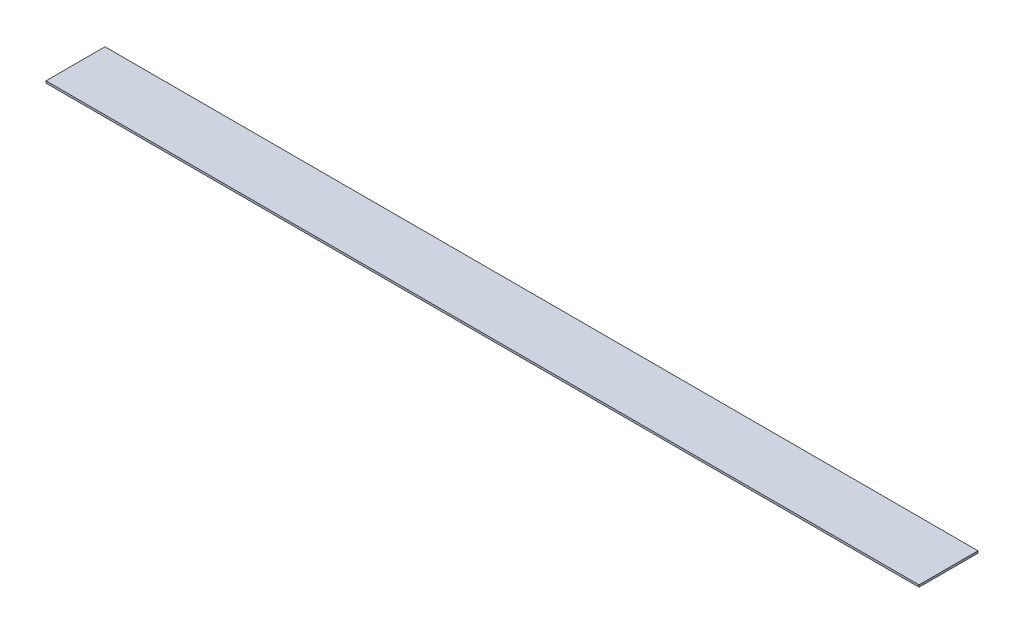
SolidWorks part; units mm, degrees
material "201 Annealed Stainless Steel (SS)"
ref_plane "Front Plane" through (0, 0, 0) normal (0, 0, 1) x (1, 0, 0)
ref_plane "Top Plane" through (0, 0, 0) normal (0, 1, 0) x (1, 0, 0)
ref_plane "Right Plane" through (0, 0, 0) normal (1, 0, 0) x (0, 0, -1)
sketch "Sketch1" plane through (0, 0, 0) normal (0, 1, 0) x (1, 0, 0)
  line L0 (234.7, 12.8) -> (234.7, -12.8) construction
  line L1 (-240, -12.8) -> (240, -12.8)
  line L2 (-240, -12.8) -> (-240, 12.8)
  line L3 (-240, 12.8) -> (240, 12.8)
  line L4 (240, -12.8) -> (240, 12.8)
  line L5 (-240, -12.8) -> (240, 12.8) construction
  line L6 (-240, 12.8) -> (240, -12.8) construction
  circle A0 centre (230.9, 0) radius 3.8
  arc A1 (234.7, 12.8) -> (234.7, -12.8) centre (221.8934, 0) cw
  point P0 (0, 0)
  dimension "D3" = 7.6
  dimension "D4" = 5.3
  dimension "D1" = 25.6
  dimension "D2" = 480
extrude "Boss-Extrude1" add sketch "Sketch1" along normal blind 0.9 contours A1 L3 L2 L1 A0
ref_plane "Plane1" through (240, 0, 0) normal (1, 0, 0) x (0, 0, -1)
sketch "Sketch2" plane through (240, 0, 0) normal (1, 0, 0) x (0, 0, -1)
  line L1 (-12.8, 0.9) -> (12.8, 0.9)
  line L2 (-12.8, 0.9) -> (-12.8, 0)
  line L3 (-12.8, 0) -> (12.8, 0)
  line L4 (12.8, 0.9) -> (12.8, 0)
extrude "Cut-Extrude1" cut sketch "Sketch2" against normal blind 101
